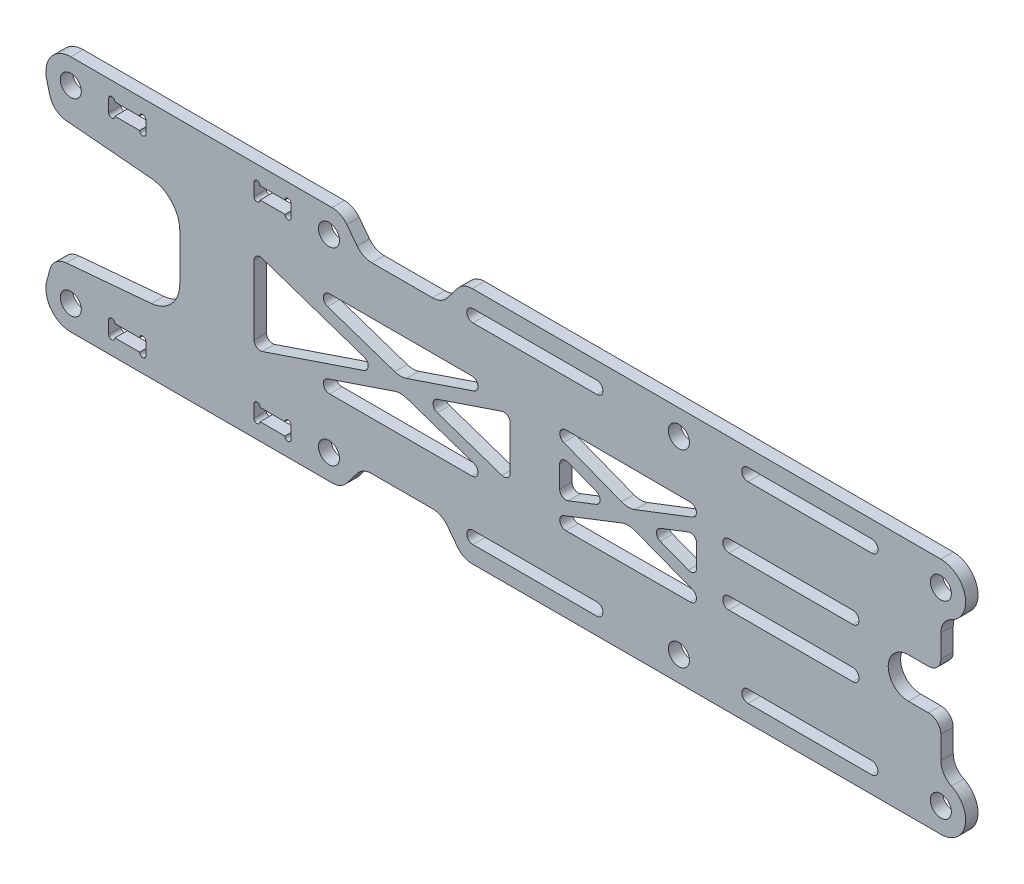
SolidWorks part; units mm, degrees
material "Thornel Mat VMA"
ref_plane "Front Plane" through (0, 0, 0) normal (0, 0, 1) x (1, 0, 0)
ref_plane "Top Plane" through (0, 0, 0) normal (0, 1, 0) x (1, 0, 0)
ref_plane "Right Plane" through (0, 0, 0) normal (1, 0, 0) x (0, 0, -1)
sketch "Sketch1" plane through (0, 0, 0) normal (0, 0, 1) x (1, 0, 0)
  line L4 (-59.8318, -16.5) -> (-63.8318, -16.5)
  line L5 (-64.8318, -16.5) -> (-64.8318, -14.5)
  line L6 (-63.8318, -14.5) -> (-59.8318, -14.5)
  line L7 (-58.8318, -14.5) -> (-58.8318, -16.5)
  line L10 (-59.8318, 16.5) -> (-63.8318, 16.5)
  line L11 (-64.8318, 16.5) -> (-64.8318, 14.5)
  line L12 (-63.8318, 14.5) -> (-59.8318, 14.5)
  line L13 (-58.8318, 14.5) -> (-58.8318, 16.5)
  line L14 (-36.3681, -16.5) -> (-40.3681, -16.5)
  line L15 (-41.3681, -16.5) -> (-41.3681, -14.5)
  line L16 (-40.3681, -14.5) -> (-36.3681, -14.5)
  line L17 (-35.3681, -14.5) -> (-35.3681, -16.5)
  line L18 (-36.3681, 16.5) -> (-40.3681, 16.5)
  line L19 (-41.3681, 16.5) -> (-41.3681, 14.5)
  line L20 (-40.3681, 14.5) -> (-36.3681, 14.5)
  line L21 (-35.3681, 14.5) -> (-35.3681, 16.5)
  line L24 (-70.9498, 19.25) -> (-28.7512, 19.25)
  line L25 (-22.3373, 14.7503) -> (-12.527, 14.7503)
  line L26 (-6.113, 19.25) -> (69.5603, 19.25)
  line L27 (69.5603, 8.9254) -> (69.5603, 5.25)
  line L28 (67.5603, 3.25) -> (64.3092, 3.25)
  line L29 (64.3092, -3.25) -> (67.5603, -3.25)
  line L30 (69.5603, -5.25) -> (69.5603, -8.9254)
  line L31 (69.5603, -19.25) -> (-6.113, -19.25)
  line L32 (-28.7512, -19.25) -> (-70.9498, -19.25)
  line L35 (-71.6862, -9.9466) -> (-57.9122, -8.7415)
  line L36 (-53.348, -3.7605) -> (-53.348, 3.7605)
  line L37 (-57.9122, 8.7415) -> (-71.6862, 9.9466)
  line L38 (-74.3225, 12.1587) -> (-74.9498, 14.5)
  line L39 (-74.9498, 14.5) -> (-74.9498, 15.25)
  line L40 (-41.348, 5.5656) -> (-41.348, -5.5656)
  line L41 (-40.0273, -6.5128) -> (-23.5895, -0.9472)
  line L42 (-23.5895, 0.9472) -> (-40.0273, 6.5128)
  line L46 (-29.479, 5.0528) -> (-18.6361, 1.3815)
  line L47 (-16.7119, 1.3815) -> (-5.869, 5.0528)
  line L48 (-6.1897, 7) -> (-29.1583, 7)
  line L49 (-11.7584, -0.9472) -> (-1.3207, -4.4813)
  line L50 (0, -3.5341) -> (0, 3.5341)
  line L51 (-1.3207, 4.4813) -> (-11.7584, 0.9472)
  line L52 (8.6503, 5.116) -> (17.9991, 1.4793)
  line L53 (20.1658, 1.476) -> (29.4469, 5.0539)
  line L54 (29.0902, 6.987) -> (9.0159, 7.0479)
  line L59 (8, 1.761) -> (8, -1.761)
  line L60 (9.3625, -2.6929) -> (13.8895, -0.932)
  line L61 (13.8895, 0.932) -> (9.3625, 2.6929)
  line L62 (30.1313, 1.7538) -> (30.1313, -1.7538)
  line L63 (28.8059, -2.6634) -> (24.2564, -0.9095)
  line L64 (24.2564, 0.9095) -> (28.8059, 2.6634)
  line L69 (0, 0) -> (50000, 0) construction
  line L70 (-16.7119, -1.3815) -> (-5.869, -5.0528)
  line L71 (-6.1897, -7) -> (-29.1583, -7)
  line L72 (-29.479, -5.0528) -> (-18.6361, -1.3815)
  line L73 (8.6503, -5.116) -> (17.9991, -1.4793)
  line L74 (20.1658, -1.476) -> (29.4469, -5.0539)
  line L75 (29.0902, -6.987) -> (9.0159, -7.0479)
  line L76 (-26.3724, 18.0779) -> (-24.7162, 15.9224)
  line L77 (-10.1481, 15.9224) -> (-8.4919, 18.0779)
  line L80 (-10.1481, -15.9224) -> (-8.4919, -18.0779)
  line L81 (-26.3724, -18.0779) -> (-24.7162, -15.9224)
  line L82 (-22.3373, -14.7503) -> (-12.527, -14.7503)
  line L83 (-74.9498, -14.5) -> (-74.9498, -15.25)
  line L84 (-74.3225, -12.1587) -> (-74.9498, -14.5)
  line L85 (35.3391, 4) -> (55.3391, 4) construction
  line L86 (35.3391, 5) -> (55.3391, 5)
  line L87 (35.3391, 3) -> (55.3391, 3)
  line L88 (35.3391, -4) -> (55.3391, -4) construction
  line L89 (35.3391, -5) -> (55.3391, -5)
  line L90 (35.3391, -3) -> (55.3391, -3)
  line L91 (38.4052, 15.5) -> (58.4052, 15.5) construction
  line L92 (38.4052, 16.5) -> (58.4052, 16.5)
  line L93 (38.4052, 14.5) -> (58.4052, 14.5)
  line L94 (-6.0048, 15.5) -> (13.9952, 15.5) construction
  line L95 (-6.0048, 16.5) -> (13.9952, 16.5)
  line L96 (-6.0048, 14.5) -> (13.9952, 14.5)
  line L97 (38.4052, 15.5) -> (-6.0048, 15.5) construction
  line L98 (-6.0048, -15.5) -> (13.9952, -15.5) construction
  line L99 (-6.0048, -16.5) -> (13.9952, -16.5)
  line L100 (-6.0048, -14.5) -> (13.9952, -14.5)
  line L101 (38.4052, -15.5) -> (58.4052, -15.5) construction
  line L102 (38.4052, -16.5) -> (58.4052, -16.5)
  line L103 (38.4052, -14.5) -> (58.4052, -14.5)
  arc A6 (-26.3724, 18.0779) -> (-28.7512, 19.25) centre (-28.7512, 16.25) ccw
  arc A8 (-24.7162, 15.9224) -> (-22.3373, 14.7503) centre (-22.3373, 17.7503) ccw
  arc A9 (71.2746, 11.636) -> (69.5603, 19.25) centre (69.5603, 15.25) ccw
  arc A10 (71.2746, 11.636) -> (69.5603, 8.9254) centre (72.5603, 8.9254) ccw
  arc A11 (67.5603, 3.25) -> (69.5603, 5.25) centre (67.5603, 5.25) ccw
  arc A12 (64.3092, 3.25) -> (64.3092, -3.25) centre (64.3092, 0) ccw
  arc A13 (69.5603, -5.25) -> (67.5603, -3.25) centre (67.5603, -5.25) ccw
  arc A14 (69.5603, -8.9254) -> (71.2746, -11.636) centre (72.5603, -8.9254) ccw
  arc A15 (69.5603, -19.25) -> (71.2746, -11.636) centre (69.5603, -15.25) ccw
  arc A18 (-57.9122, -8.7415) -> (-53.348, -3.7605) centre (-58.348, -3.7605) ccw
  arc A19 (-53.348, 3.7605) -> (-57.9122, 8.7415) centre (-58.348, 3.7605) ccw
  arc A20 (-74.3225, 12.1587) -> (-71.6862, 9.9466) centre (-71.4247, 12.9352) ccw
  arc A21 (-70.9498, 19.25) -> (-74.9498, 15.25) centre (-70.9498, 15.25) ccw
  arc A24 (-12.527, 14.7503) -> (-10.1481, 15.9224) centre (-12.527, 17.7503) ccw
  arc A25 (-6.113, 19.25) -> (-8.4919, 18.0779) centre (-6.113, 16.25) ccw
  arc A37 (-59.8318, -16.5) -> (-58.8318, -16.5) centre (-59.3318, -16.5) ccw
  arc A38 (-64.8318, -16.5) -> (-63.8318, -16.5) centre (-64.3318, -16.5) ccw
  arc A39 (-63.8318, -14.5) -> (-64.8318, -14.5) centre (-64.3318, -14.5) ccw
  arc A40 (-58.8318, -14.5) -> (-59.8318, -14.5) centre (-59.3318, -14.5) ccw
  arc A43 (-58.8318, 16.5) -> (-59.8318, 16.5) centre (-59.3318, 16.5) ccw
  arc A44 (-63.8318, 16.5) -> (-64.8318, 16.5) centre (-64.3318, 16.5) ccw
  arc A45 (-64.8318, 14.5) -> (-63.8318, 14.5) centre (-64.3318, 14.5) ccw
  arc A46 (-59.8318, 14.5) -> (-58.8318, 14.5) centre (-59.3318, 14.5) ccw
  arc A47 (-36.3681, -16.5) -> (-35.3681, -16.5) centre (-35.8681, -16.5) ccw
  arc A48 (-41.3681, -16.5) -> (-40.3681, -16.5) centre (-40.8681, -16.5) ccw
  arc A49 (-40.3681, -14.5) -> (-41.3681, -14.5) centre (-40.8681, -14.5) ccw
  arc A50 (-35.3681, -14.5) -> (-36.3681, -14.5) centre (-35.8681, -14.5) ccw
  arc A51 (-35.3681, 16.5) -> (-36.3681, 16.5) centre (-35.8681, 16.5) ccw
  arc A52 (-40.3681, 16.5) -> (-41.3681, 16.5) centre (-40.8681, 16.5) ccw
  arc A53 (-41.3681, 14.5) -> (-40.3681, 14.5) centre (-40.8681, 14.5) ccw
  arc A54 (-36.3681, 14.5) -> (-35.3681, 14.5) centre (-35.8681, 14.5) ccw
  arc A57 (-41.348, -5.5656) -> (-40.0273, -6.5128) centre (-40.348, -5.5656) ccw
  arc A58 (-23.5895, -0.9472) -> (-23.5895, 0.9472) centre (-23.9102, 0) ccw
  arc A59 (-40.0273, 6.5128) -> (-41.348, 5.5656) centre (-40.348, 5.5656) ccw
  arc A63 (-18.6361, 1.3815) -> (-16.7119, 1.3815) centre (-17.674, 4.2231) ccw
  arc A64 (-5.869, 5.0528) -> (-6.1897, 7) centre (-6.1897, 6) ccw
  arc A65 (-29.1583, 7) -> (-29.479, 5.0528) centre (-29.1583, 6) ccw
  arc A66 (-1.3207, -4.4813) -> (0, -3.5341) centre (-1, -3.5341) ccw
  arc A67 (0, 3.5341) -> (-1.3207, 4.4813) centre (-1, 3.5341) ccw
  arc A68 (-11.7584, 0.9472) -> (-11.7584, -0.9472) centre (-11.4377, 0) ccw
  arc A69 (9.0159, 7.0479) -> (8.6503, 5.116) centre (9.0129, 6.048) ccw
  arc A70 (17.9991, 1.4793) -> (20.1658, 1.476) centre (19.0867, 4.2752) ccw
  arc A71 (29.4469, 5.0539) -> (29.0902, 6.987) centre (29.0872, 5.987) ccw
  arc A75 (8, -1.761) -> (9.3625, -2.6929) centre (9, -1.761) ccw
  arc A76 (13.8895, -0.932) -> (13.8895, 0.932) centre (13.527, 0) ccw
  arc A77 (9.3625, 2.6929) -> (8, 1.761) centre (9, 1.761) ccw
  arc A78 (28.8059, -2.6634) -> (30.1313, -1.7538) centre (29.1565, -1.7538) ccw
  arc A79 (24.2564, 0.9095) -> (24.2564, -0.9095) centre (24.6071, 0) ccw
  arc A80 (30.1313, 1.7538) -> (28.8059, 2.6634) centre (29.1565, 1.7538) ccw
  arc A85 (-5.869, -5.0528) -> (-6.1897, -7) centre (-6.1897, -6) cw
  arc A86 (-29.1583, -7) -> (-29.479, -5.0528) centre (-29.1583, -6) cw
  arc A87 (-18.6361, -1.3815) -> (-16.7119, -1.3815) centre (-17.674, -4.2231) cw
  arc A88 (17.9991, -1.4793) -> (20.1658, -1.476) centre (19.0867, -4.2752) cw
  arc A89 (9.0159, -7.0479) -> (8.6503, -5.116) centre (9.0129, -6.048) cw
  arc A90 (29.4469, -5.0539) -> (29.0902, -6.987) centre (29.0872, -5.987) cw
  arc A91 (-26.3724, -18.0779) -> (-28.7512, -19.25) centre (-28.7512, -16.25) cw
  arc A92 (-6.113, -19.25) -> (-8.4919, -18.0779) centre (-6.113, -16.25) cw
  arc A93 (-12.527, -14.7503) -> (-10.1481, -15.9224) centre (-12.527, -17.7503) cw
  arc A94 (-24.7162, -15.9224) -> (-22.3373, -14.7503) centre (-22.3373, -17.7503) cw
  arc A95 (-74.3225, -12.1587) -> (-71.6862, -9.9466) centre (-71.4247, -12.9352) cw
  arc A96 (-70.9498, -19.25) -> (-74.9498, -15.25) centre (-70.9498, -15.25) cw
  arc A97 (35.3391, 5) -> (35.3391, 3) centre (35.3391, 4) ccw
  arc A98 (55.3391, 3) -> (55.3391, 5) centre (55.3391, 4) ccw
  arc A99 (35.3391, -5) -> (35.3391, -3) centre (35.3391, -4) cw
  arc A100 (55.3391, -3) -> (55.3391, -5) centre (55.3391, -4) cw
  arc A101 (38.4052, 16.5) -> (38.4052, 14.5) centre (38.4052, 15.5) ccw
  arc A102 (58.4052, 14.5) -> (58.4052, 16.5) centre (58.4052, 15.5) ccw
  arc A103 (-6.0048, 16.5) -> (-6.0048, 14.5) centre (-6.0048, 15.5) ccw
  arc A104 (13.9952, 14.5) -> (13.9952, 16.5) centre (13.9952, 15.5) ccw
  arc A105 (-6.0048, -16.5) -> (-6.0048, -14.5) centre (-6.0048, -15.5) cw
  arc A106 (13.9952, -14.5) -> (13.9952, -16.5) centre (13.9952, -15.5) cw
  arc A107 (38.4052, -16.5) -> (38.4052, -14.5) centre (38.4052, -15.5) cw
  arc A108 (58.4052, -14.5) -> (58.4052, -16.5) centre (58.4052, -15.5) cw
  point P2 (0, 0)
  point P73 (-53.348, 0)
  point P77 (0, 0)
  point P78 (-53.5716, 11.3633)
  point P79 (-53.8995, 12.0191)
  point P80 (30.1313, -1.7538)
  point P83 (3.9952, -15.5)
  point P101 (-41.2604, 13.1392)
  point P105 (3.9952, 15.5)
  point P145 (48.4052, 15.5)
  point P158 (8, 0)
  point P159 (45.3391, 4)
  point P198 (30.1313, 0)
  point P221 (45.3391, -4)
  point P232 (48.4052, -15.5)
  point P239 (0, 0)
  point P240 (-40.0273, -5.5656)
  dimension "D1" = 3
  dimension "D2" = 1
  dimension "D8" = 1
  dimension "D13" = 1
  dimension "D6" = 1
  dimension "D19" = 1
  dimension "D20" = 3
  dimension "D25" = 0.9748
  dimension "D27" = 4
  dimension "D28" = 3
  dimension "D29" = 2
  dimension "D30" = 3.25
  dimension "D36" = 3
  dimension "D37" = 4
  dimension "D45" = 3
  dimension "D49" = 5
  dimension "D3" = 2
  dimension "D4" = 2
  dimension "D5" = 2
  dimension "D7" = 2
  dimension "D9" = 1.3207
  dimension "D10" = 11.4377
  dimension "D11" = 5.869
  dimension "D12" = 16.7119
  dimension "D14" = 23.5895
  dimension "D15" = 40.0273
  dimension "D16" = 8
  dimension "D17" = 9.3625
  dimension "D18" = 13.527
  dimension "D21" = 8.6503
  dimension "D22" = 9.0159
  dimension "D23" = 17.9991
  dimension "D24" = 20.1658
  dimension "D26" = 28.8059
  dimension "D31" = 64.3092
  dimension "D32" = 69.5603
  dimension "D33" = 3.25
  dimension "D34" = 8.9254
  dimension "D35" = 6.113
  dimension "D38" = 28.7512
  dimension "D39" = 57.9122
  dimension "D40" = 71.4247
  dimension "D41" = 71.6862
  dimension "D42" = 74.3225
  dimension "D43" = 74.9498
  dimension "D44" = 8.7415
  dimension "D46" = 8.4919
  dimension "D47" = 10.1481
  dimension "D48" = 19.25
  dimension "D50" = 2
  dimension "D51" = 20
  dimension "D52" = 45.3391
  dimension "D53" = 4
  dimension "D54" = 2
  dimension "D55" = 20
  dimension "D56" = 38.4052
  dimension "D57" = 15.5
  dimension "D58" = 2
  dimension "D59" = 44.41
extrude "Boss-Extrude1" add sketch "Sketch1" along normal blind 2
hole_wizard "M3 Clearance Hole1" positions "Sketch2" profile "Sketch3" hole size "M3" standard "ANSI Metric" end condition up to next
sketch "Sketch2" plane through (0, 0, 2) normal (0, 0, 1) x (1, 0, 0)
  line L4 (-70.9498, 15.25) -> (69.5603, 15.25) construction
  line L6 (-29.25, 15.25) -> (-29.25, -15.25) construction
  line L8 (27.25, -15.25) -> (27.25, 15.25) construction
  line L11 (-70.9498, -15.25) -> (69.5603, -15.25) construction
  arc A0 (-74.9498, -15.25) -> (-70.9498, -19.25) centre (-70.9498, -15.25) ccw construction
  point P0 (-70.9498, 15.25)
  point P3 (-70.9498, -15.25)
  point P6 (-29.25, -15.25)
  point P9 (-29.25, 15.25)
  point P12 (27.25, 15.25)
  point P15 (27.25, -15.25)
  point P18 (69.5603, -15.25)
  point P21 (69.5603, 15.25)
  point P58 (0, 0)
  point P62 (0, 0)
  point P63 (-70.9498, -15.25)
  dimension "D1" = 41.6998
  dimension "D2" = 56.5
sketch "Sketch3" plane through (-70.9498, 15.25, 2) normal (1, 0, 0) x (0, -1, 0)
  line L0 (0, 0) -> (0, 2)
  line L1 (0, 2) -> (1.7, 2)
  line L2 (1.7, 2) -> (1.7, 0)
  line L5 (1.7, 0) -> (0, 0)
  line L11 (0, -6.35) -> (0, 107.95) construction
  dimension "Thru Hole Dia." = 3.4
  dimension "Thru Hole Depth" = 2
